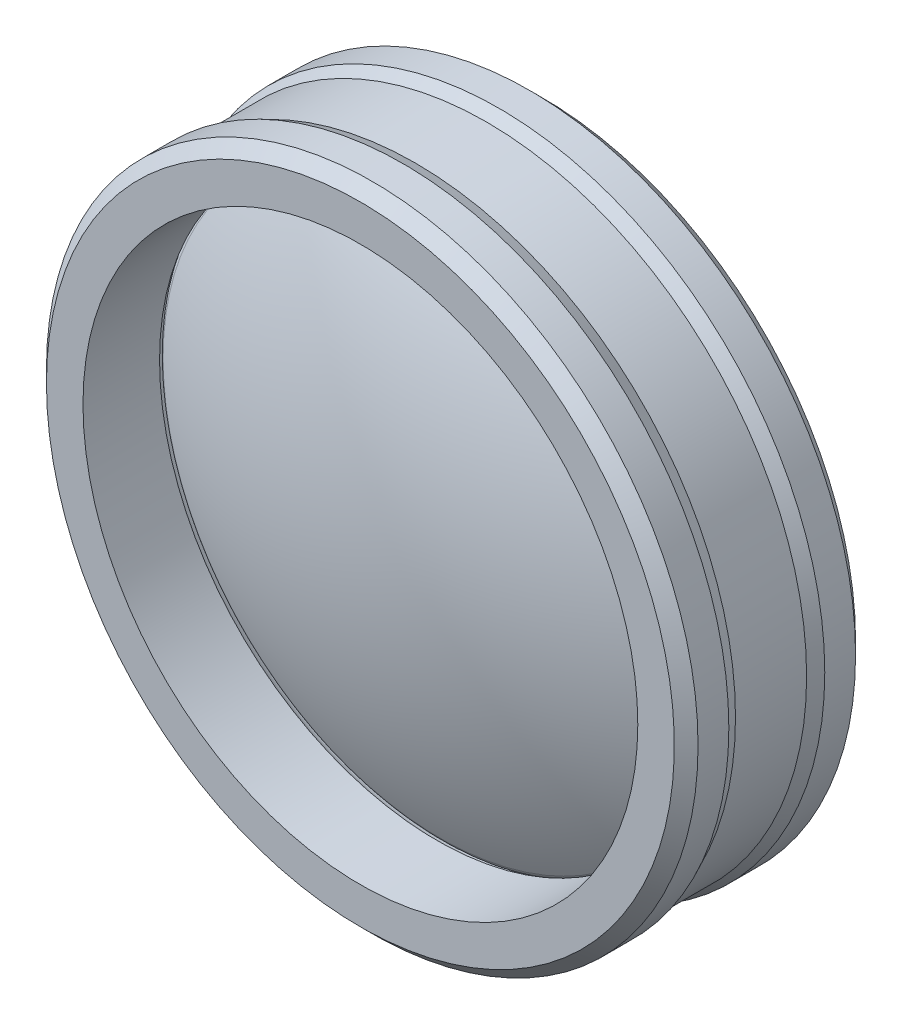
SolidWorks part; units mm, degrees
ref_plane "Front Plane" through (0, 0, 0) normal (0, 0, 1) x (1, 0, 0)
ref_plane "Top Plane" through (0, 0, 0) normal (0, 1, 0) x (1, 0, 0)
ref_plane "Right Plane" through (0, 0, 0) normal (1, 0, 0) x (0, 0, -1)
sketch "Sketch1" plane through (0, 0, 0) normal (1, 0, 0) x (0, 0, -1)
  line L0 (-86.576, 0) -> (96.4864, 0) construction
  line L1 (0, -71.8973) -> (0, 70.7754) construction
  line L2 (-6.6987, 0) -> (6.6987, 0)
  arc A0 (0, 25) -> (6.6987, 0) centre (-43.3013, 0) cw
  arc A1 (0, 25) -> (-6.6987, 0) centre (43.3013, 0) ccw
  dimension "D1" = 50
  dimension "D2" = 50
  dimension "D3" = 25
revolve "Revolve3" add sketch "Sketch1" angle 360 about L0
fillet "Fillet1" radius 1 1 edges at (25, 0, 0)
sketch "Sketch2" plane through (0, 0, 0) normal (1, 0, 0) x (0, 0, -1)
  line L0 (-1.1836, 23.4027) -> (-7.6442, 23.4027)
  line L1 (-7.6442, 23.4027) -> (-7.6442, 27.485)
  line L2 (-7.6442, 27.485) -> (-4.0467, 27.485)
  line L3 (7.6442, 27.485) -> (7.6442, 23.4027)
  line L4 (7.6442, 23.4027) -> (1.1836, 23.4027)
  line L5 (7.6442, 23.4027) -> (7.6442, -24.984) construction
  line L6 (0, 0) -> (25.7364, 0) construction
  line L7 (4.0467, 27.485) -> (3, 27)
  line L8 (3, 27) -> (-3, 27)
  line L9 (-3, 27) -> (-4.0467, 27.485)
  line L10 (4.0467, 27.485) -> (7.6442, 27.485)
  arc A0 (0.8837, 23.4027) -> (-0.8837, 23.4027) centre (0, 22.9347) ccw construction
  arc A1 (0.8837, 23.4027) -> (-0.8837, 23.4027) centre (0, 22.9347) ccw construction
  arc A2 (-1.1836, 23.4027) -> (1.1836, 23.4027) centre (0, 22.9347) cw
  point P18 (5.1789, 26.187)
  point P19 (4.0467, 25.575)
  dimension "D1" = 6
  dimension "D2" = 27
revolve "Revolve5" add sketch "Sketch2" angle 360 about L6
chamfer "Chamfer1" distance 1 angle 45 2 edges at (27.485, 0, 7.6442) (27.485, 0, -7.6442)
sketch "Sketch3" plane through (0, 0, 0) normal (0, 0, 1) x (1, 0, 0)
  circle A0 centre (0, 0) radius 27 construction
  circle A1 centre (0, 0) radius 27 construction
sketch "Sketch4" plane through (0, 0, 0) normal (0, 1, 0) x (1, 0, 0)
  line L0 (-27, 3) -> (-27, -3) construction
  line L1 (-27, 3) -> (-27, -3)
  dimension "D1" = 6
